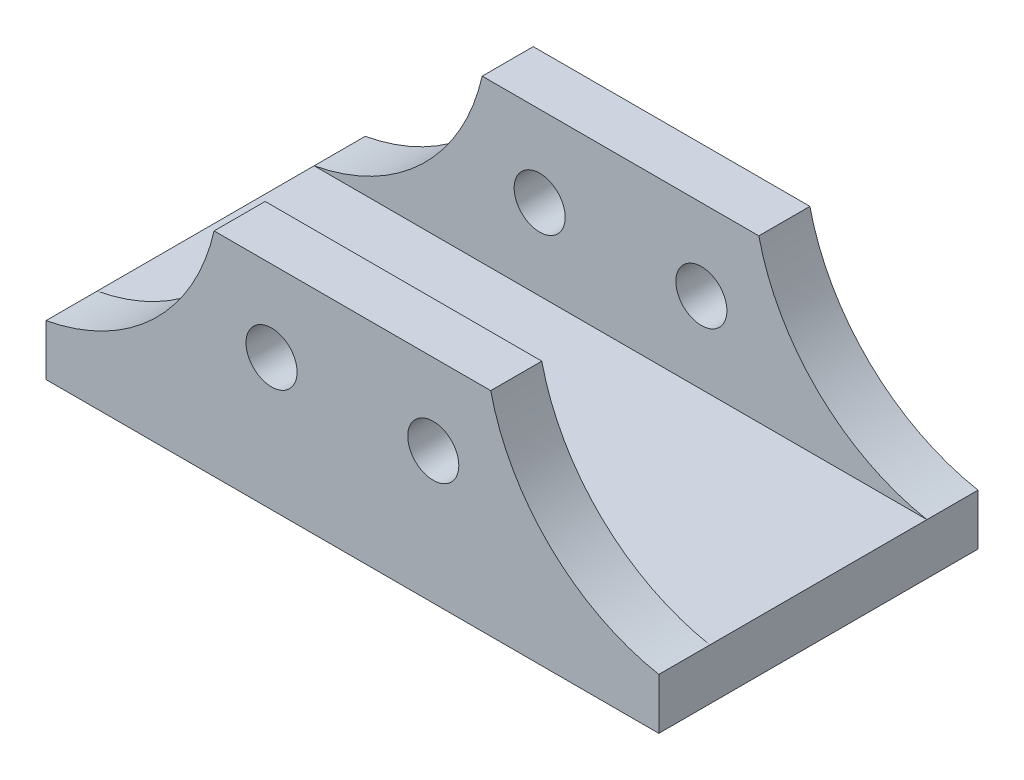
SolidWorks part; units mm, degrees
ref_plane "Front Plane" through (0, 0, 0) normal (0, 0, 1) x (1, 0, 0)
ref_plane "Top Plane" through (0, 0, 0) normal (0, 1, 0) x (1, 0, 0)
ref_plane "Right Plane" through (0, 0, 0) normal (1, 0, 0) x (0, 0, -1)
sketch "Sketch1" plane through (0, 0, 0) normal (0, 0, 1) x (1, 0, 0)
  line L0 (0, 0) -> (0, 50) construction
  line L1 (-32.5, 50) -> (32.5, 50)
  line L2 (-72, 0) -> (72, 0)
  line L3 (72, 12) -> (72, 0)
  line L4 (-72, 12) -> (-72, 0)
  arc A0 (32.5, 50) -> (72, 12) centre (81.2436, 61.1381) ccw
  circle A1 centre (19, 31) radius 6
  circle A2 centre (-19, 31) radius 6
  arc A3 (-32.5, 50) -> (-72, 12) centre (-81.2436, 61.1381) cw
  dimension "D5" = 50
  dimension "D6" = 12
  dimension "D1" = 72
  dimension "D2" = 12
  dimension "D3" = 32.5
  dimension "D4" = 50
  dimension "D7" = 31
  dimension "D8" = 19
extrude "Boss-Extrude2" add sketch "Sketch1" along normal blind 12 contours A1 | A2 | A3 L4 L2 L3 A0 L1
ref_plane "Plane2" through (0, 0, 37.5) normal (0, 0, 1) x (1, 0, 0)
mirror "Mirror1" about plane through (0, 0, 37.5) normal (0, 0, 1) of bodies 102
sketch "Sketch3" plane through (0, 0, 37.5) normal (0, 0, 1) x (1, 0, 0)
  line L1 (-72, 0) -> (72, 0)
  line L2 (-72, 0) -> (-72, 12)
  line L3 (-72, 12) -> (72, 12)
  line L4 (72, 0) -> (72, 12)
extrude "Boss-Extrude3" add sketch "Sketch3" along normal blind 25.5 and the other way blind 25.5
